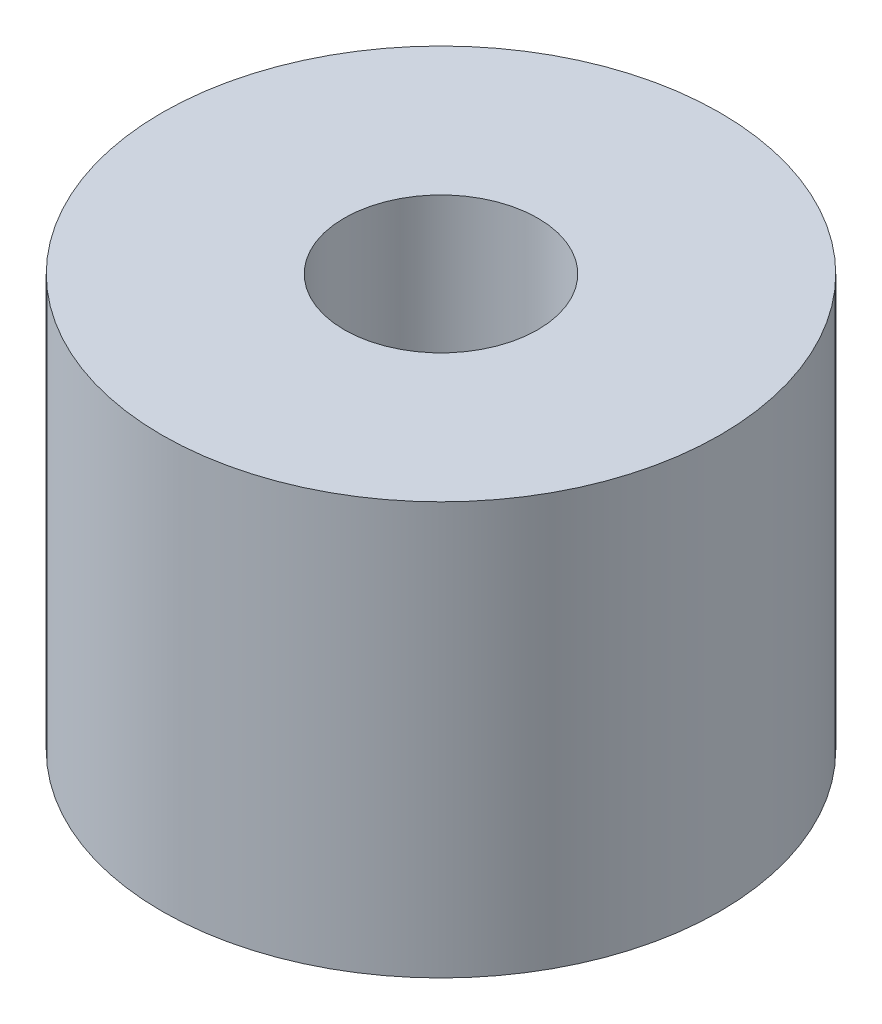
SolidWorks part; units mm, degrees
ref_plane "Front Plane" through (0, 0, 0) normal (0, 0, 1) x (1, 0, 0)
ref_plane "Top Plane" through (0, 0, 0) normal (0, 1, 0) x (1, 0, 0)
ref_plane "Right Plane" through (0, 0, 0) normal (1, 0, 0) x (0, 0, -1)
sketch "Croquis1" plane through (0, 0, 0) normal (0, 1, 0) x (1, 0, 0)
  circle A0 centre (0, 0) radius 7.5
  circle A1 centre (0, 0) radius 2.6
  dimension "D1" = 15
  dimension "D2" = 5.2
extrude "Saliente-Extruir1" add sketch "Croquis1" along normal blind 11.08
